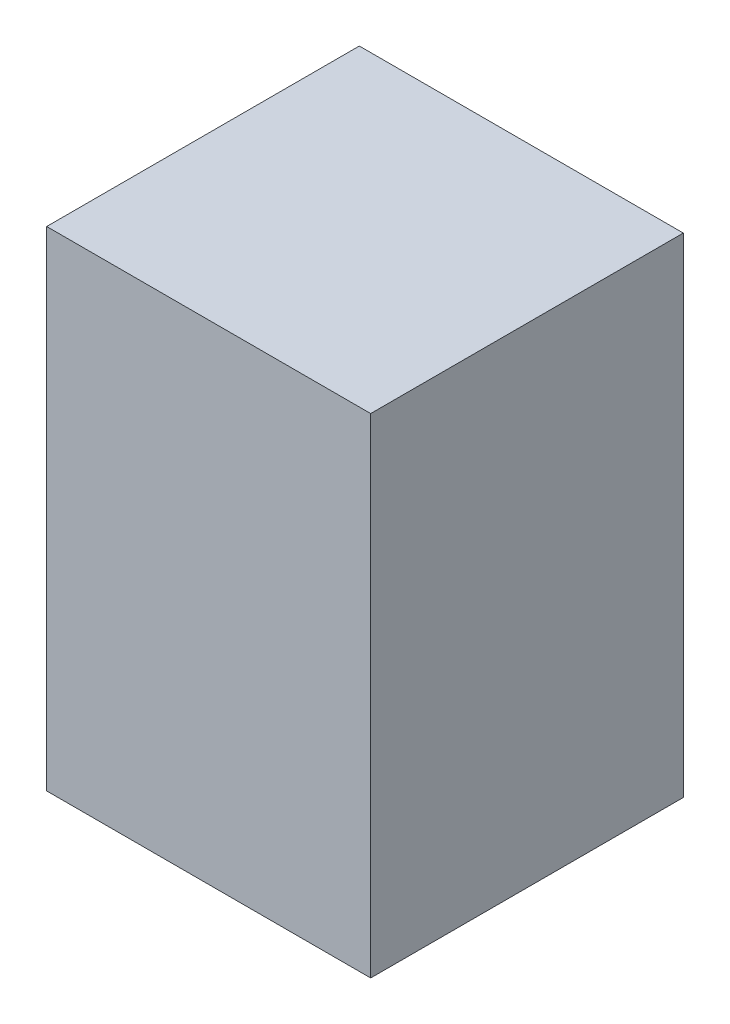
SolidWorks part; units mm, degrees
ref_plane "Front Plane" through (0, 0, 0) normal (0, 0, 1) x (1, 0, 0)
ref_plane "Top Plane" through (0, 0, 0) normal (0, 1, 0) x (1, 0, 0)
ref_plane "Right Plane" through (0, 0, 0) normal (1, 0, 0) x (0, 0, -1)
sketch "Sketch1" plane through (0, 0, 0) normal (0, 0, 1) x (1, 0, 0)
  line L0 (0, 0) -> (0, 86)
  line L1 (0, 86) -> (57, 86)
  line L2 (57, 86) -> (57, 0)
  line L3 (57, 0) -> (0, 0)
extrude "Boss-Extrude1" add sketch "Sketch1" along normal blind 55
sketch "Sketch3" plane through (0, 0, 0) normal (0, 0, -1) x (-1, 0, 0)
  text T0 "Bottom"
sketch "Sketch4" plane through (0, 86, 0) normal (0, 1, 0) x (1, 0, 0)
  text T0 "Ribbon" font "Century Gothic" height 3.5
sketch "Sketch5" plane through (0, 0, 0) normal (0, -1, 0) x (1, 0, 0)
  line L0 (0, 0) -> (0, 40) construction
  line L1 (0, 55) -> (0, 0) construction
  line L2 (0, 40) -> (57, 40) construction
  line L3 (57, 55) -> (57, 0) construction
  line L4 (57, 40) -> (57, 0) construction
  line L5 (57, 0) -> (0, 0) construction
  text T0 "Ports"
sketch "Sketch6" plane through (0, 0, 0) normal (-1, 0, 0) x (0, 0, 1)
  line L0 (0, 86) -> (30, 86) construction
  line L1 (30, 86) -> (30, 0) construction
  line L2 (40, 0) -> (0, 0) construction
  text T0 "HDMI"
sketch "Sketch7" plane through (0, 0, 0) normal (0, 0, -1) x (-1, 0, 0)
  circle A0 centre (-4, 1.5) radius 0.5
  circle A1 centre (-53, 1.5) radius 0.5
  circle A2 centre (-4, 84.5) radius 0.5
  circle A3 centre (-53, 84.5) radius 0.5
  point P0 (-4, 84.5)
  point P1 (-4, 1.5)
  point P2 (-53, 1.5)
  point P3 (-53, 84.5)
extrude "Cut-Extrude1" cut sketch "Sketch7" against normal blind 5
